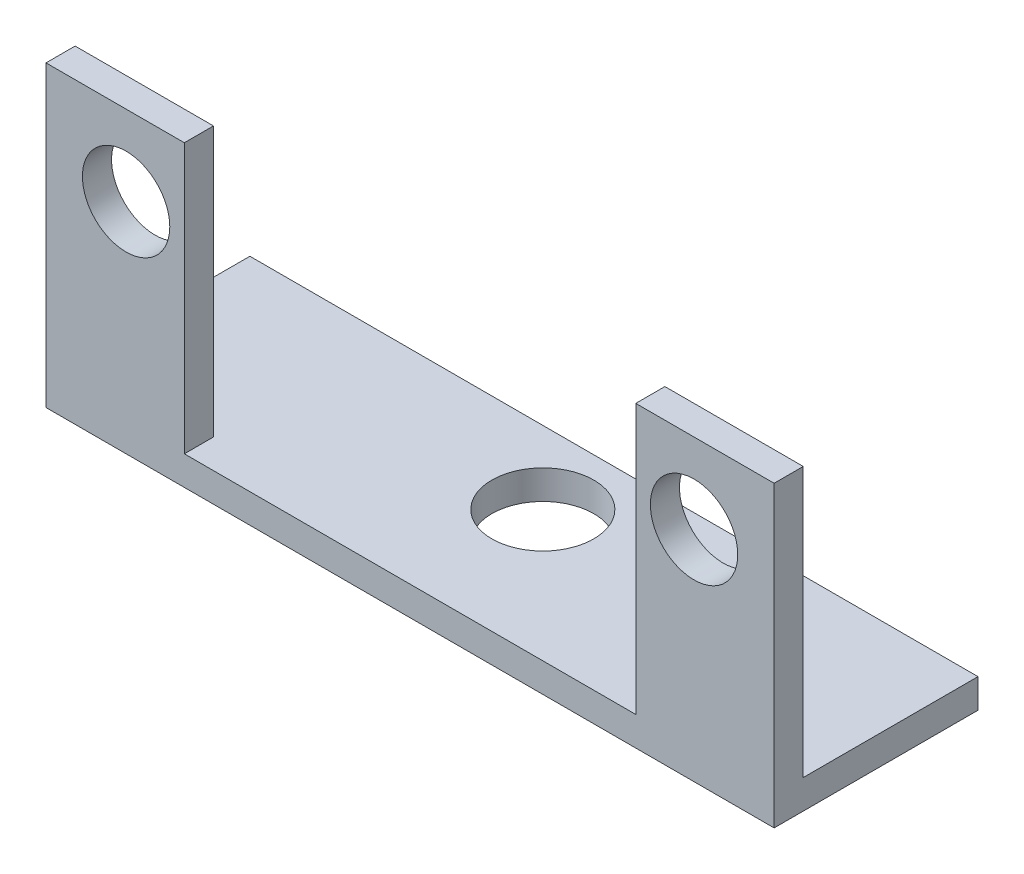
SolidWorks part; units mm, degrees
ref_plane "Plano frontal" through (0, 0, 0) normal (0, 0, 1) x (1, 0, 0)
ref_plane "Plano superior" through (0, 0, 0) normal (0, 1, 0) x (1, 0, 0)
ref_plane "Plano direito" through (0, 0, 0) normal (1, 0, 0) x (0, 0, -1)
sketch "Esboço1" plane through (0, 0, 0) normal (0, 0, 1) x (1, 0, 0)
  line L0 (-2.9307, 5.5815) -> (-2.9307, -4.6685)
  line L1 (-2.9307, -4.6685) -> (22.0693, -4.6685)
  line L2 (22.0693, -4.6685) -> (22.0693, 5.5815)
  line L3 (22.0693, 5.5815) -> (17.3193, 5.5815)
  line L4 (17.3193, 5.5815) -> (17.3193, -3.6685)
  line L5 (17.3193, -3.6685) -> (1.8193, -3.6685)
  line L6 (1.8193, -3.6685) -> (1.8193, 5.5815)
  line L7 (1.8193, 5.5815) -> (-2.9307, 5.5815)
  circle A0 centre (-0.1807, 2.8315) radius 1.5
  circle A1 centre (19.3193, 2.8315) radius 1.5
  dimension "D7" = 2
  dimension "D1" = 1
  dimension "D2" = 9.25
  dimension "D3" = 4.75
  dimension "D4" = 4.75
  dimension "D5" = 9.25
  dimension "D6" = 25
  dimension "D8" = 2.75
  dimension "D9" = 2
  dimension "D10" = 15.5
extrude "Ressalto-extrusão1" add sketch "Esboço1" along normal blind 1
sketch "Esboço2" plane through (0, 0, 0) normal (0, 0, -1) x (-1, 0, 0)
  line L0 (2.9307, 5.5815) -> (2.9307, -4.6685) construction
  line L1 (-22.0693, -4.6685) -> (2.9307, -4.6685)
  line L2 (-22.0693, -4.6685) -> (-22.0693, -3.6685)
  line L3 (-22.0693, -3.6685) -> (2.9307, -3.6685)
  line L4 (2.9307, -4.6685) -> (2.9307, -3.6685)
  line L5 (-17.3193, -3.6685) -> (-1.8193, -3.6685) construction
extrude "Ressalto-extrusão2" add sketch "Esboço2" along normal blind 6
sketch "Esboço3" plane through (0, -3.6685, 0) normal (0, 1, 0) x (1, 0, 0)
  line L0 (-2.9307, 6) -> (22.0693, 6) construction
  circle A0 centre (9.6279, 3.5) radius 1.75
  dimension "D1" = 3.5
  dimension "D2" = 2.5
extrude "Corte-extrusão1" cut sketch "Esboço3" against normal blind 5
